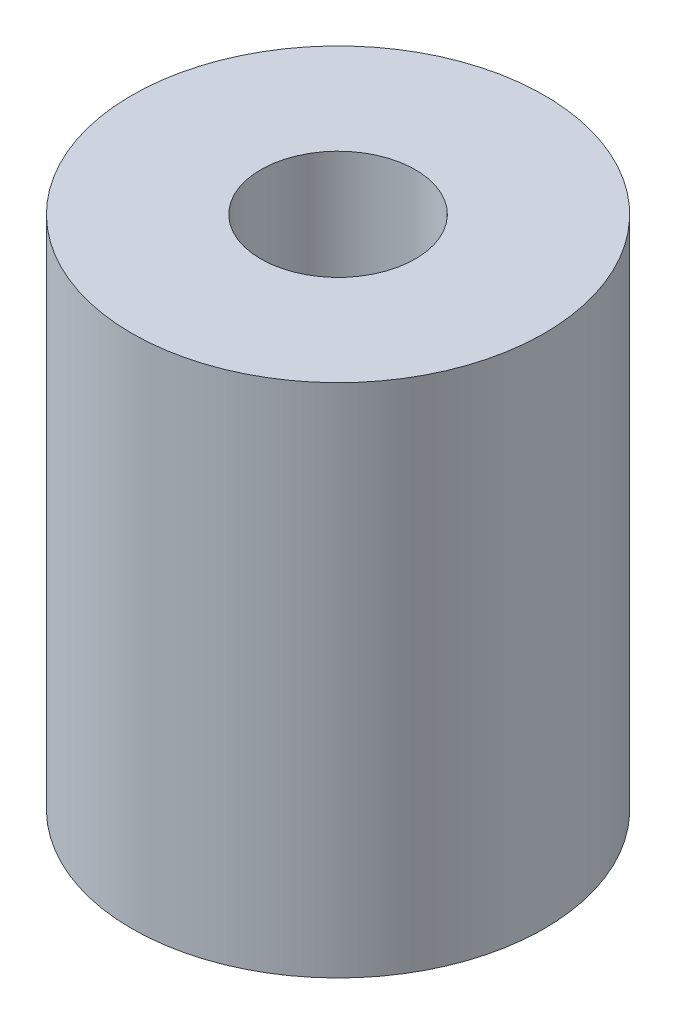
SolidWorks part; units mm, degrees
ref_plane "Front Plane" through (0, 0, 0) normal (0, 0, 1) x (1, 0, 0)
ref_plane "Top Plane" through (0, 0, 0) normal (0, 1, 0) x (1, 0, 0)
ref_plane "Right Plane" through (0, 0, 0) normal (1, 0, 0) x (0, 0, -1)
sketch "Sketch1" plane through (0, 0, 0) normal (0, 1, 0) x (1, 0, 0)
  circle A0 centre (0, 0) radius 1.5
  circle A1 centre (0, 0) radius 4
  dimension "D1" = 3
  dimension "D2" = 8
extrude "Boss-Extrude1" add sketch "Sketch1" along normal blind 10
